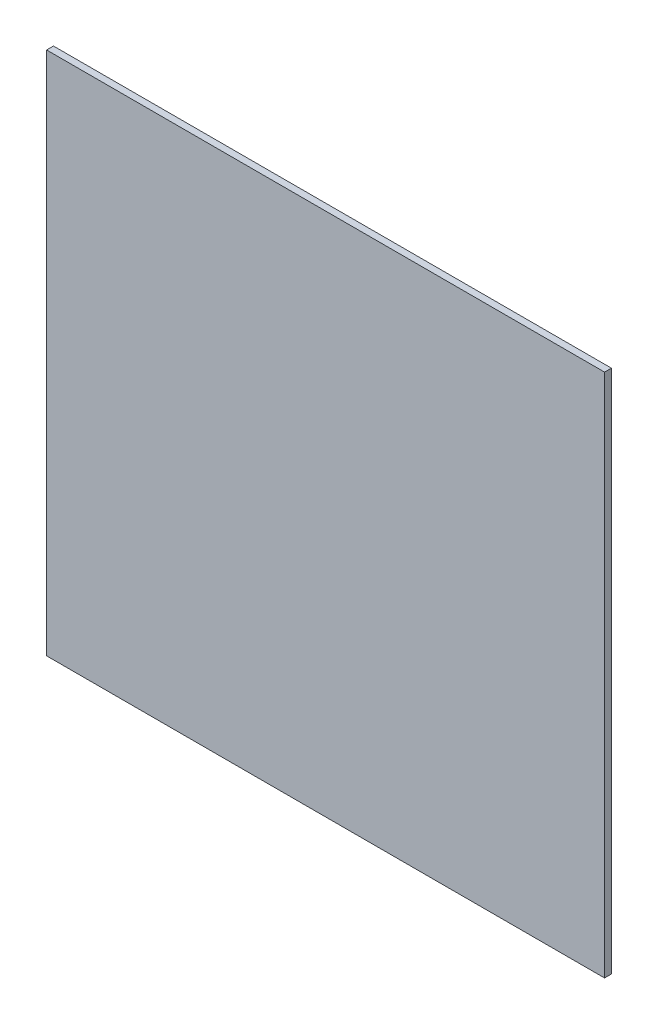
SolidWorks part; units mm, degrees
ref_plane "Front Plane" through (0, 0, 0) normal (0, 0, 1) x (1, 0, 0)
ref_plane "Top Plane" through (0, 0, 0) normal (0, 1, 0) x (1, 0, 0)
ref_plane "Right Plane" through (0, 0, 0) normal (1, 0, 0) x (0, 0, -1)
sketch "Sketch1" plane through (0, 0, 0) normal (0, 0, 1) x (1, 0, 0)
  line L0 (0, 0) -> (0, 914.4)
  line L1 (0, 0) -> (972.312, 0)
  line L2 (972.312, 0) -> (972.312, 914.4)
  line L3 (972.312, 914.4) -> (0, 914.4)
  dimension "D1" = 914.4
  dimension "D2" = 972.312
extrude "Boss-Extrude1" add sketch "Sketch1" along normal blind 11.938
